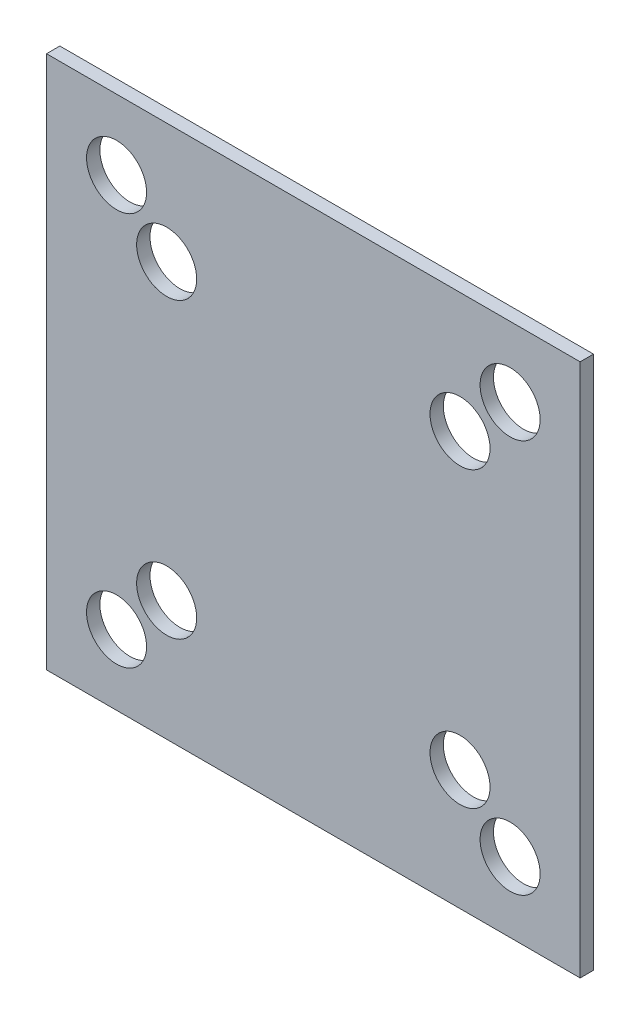
SolidWorks part; units mm, degrees
ref_plane "正面" through (0, 0, 0) normal (0, 0, 1) x (1, 0, 0)
ref_plane "平面" through (0, 0, 0) normal (0, 1, 0) x (1, 0, 0)
ref_plane "右側面" through (0, 0, 0) normal (1, 0, 0) x (0, 0, -1)
sketch "ｽｹｯﾁ1" plane through (0, 0, 0) normal (0, 0, 1) x (1, 0, 0)
  line L1 (-40, 40) -> (40, 40)
  line L2 (-40, 40) -> (-40, -40)
  line L3 (-40, -40) -> (40, -40)
  line L4 (40, 40) -> (40, -40)
  line L5 (-40, 40) -> (40, -40) construction
  line L6 (-40, -40) -> (40, 40) construction
  point P0 (0, 0)
  dimension "D1" = 80
  dimension "D2" = 80
extrude "ﾎﾞｽ - 押し出し1" add sketch "ｽｹｯﾁ1" along normal blind 2
sketch "ｽｹｯﾁ2" plane through (0, 0, 2) normal (0, 0, 1) x (1, 0, 0)
  line L1 (29.5, -29.5) -> (-29.5, -29.5)
  line L2 (29.5, -29.5) -> (29.5, 29.5)
  line L3 (29.5, 29.5) -> (-29.5, 29.5)
  line L4 (-29.5, -29.5) -> (-29.5, 29.5)
  line L5 (29.5, -29.5) -> (-29.5, 29.5) construction
  line L6 (29.5, 29.5) -> (-29.5, -29.5) construction
  line L7 (21.99, -21.99) -> (-21.99, -21.99)
  line L8 (21.99, -21.99) -> (21.99, 21.99)
  line L9 (21.99, 21.99) -> (-21.99, 21.99)
  line L10 (-21.99, -21.99) -> (-21.99, 21.99)
  line L11 (21.99, -21.99) -> (-21.99, 21.99) construction
  line L12 (21.99, 21.99) -> (-21.99, -21.99) construction
  circle A0 centre (29.5, -29.5) radius 4.5
  circle A1 centre (21.99, -21.99) radius 4.5
  circle A2 centre (29.5, 29.5) radius 4.5
  circle A3 centre (21.99, 21.99) radius 4.5
  circle A4 centre (-21.99, 21.99) radius 4.5
  circle A5 centre (-29.5, 29.5) radius 4.5
  circle A6 centre (-21.99, -21.99) radius 4.5
  circle A7 centre (-29.5, -29.5) radius 4.5
  point P0 (0, 0)
  point P6 (0, 0)
  dimension "D5" = 9
  dimension "D6" = 9
  dimension "D7" = 9
  dimension "D8" = 9
  dimension "D9" = 9
  dimension "D10" = 9
  dimension "D11" = 9
  dimension "D12" = 9
  dimension "D1" = 59
  dimension "D2" = 43.98
  dimension "D3" = 43.98
  dimension "D4" = 59
extrude "ｶｯﾄ - 押し出し1" cut sketch "ｽｹｯﾁ2" against normal blind 10 contours L1 A0 L2 | L2 A0 L1 | L7 A1 L8 | L8 A1 L7 | L2 A2 L3 | L3 A2 L2 | L8 A3 L9 | L9 A3 L8 | L10 A6 L7 | L7 A6 L10 | L1 A7 L4 | L4 A7 L1 | L10 A4 L9 | L9 A4 L10 | L4 A5 L3 | L3 A5 L4
